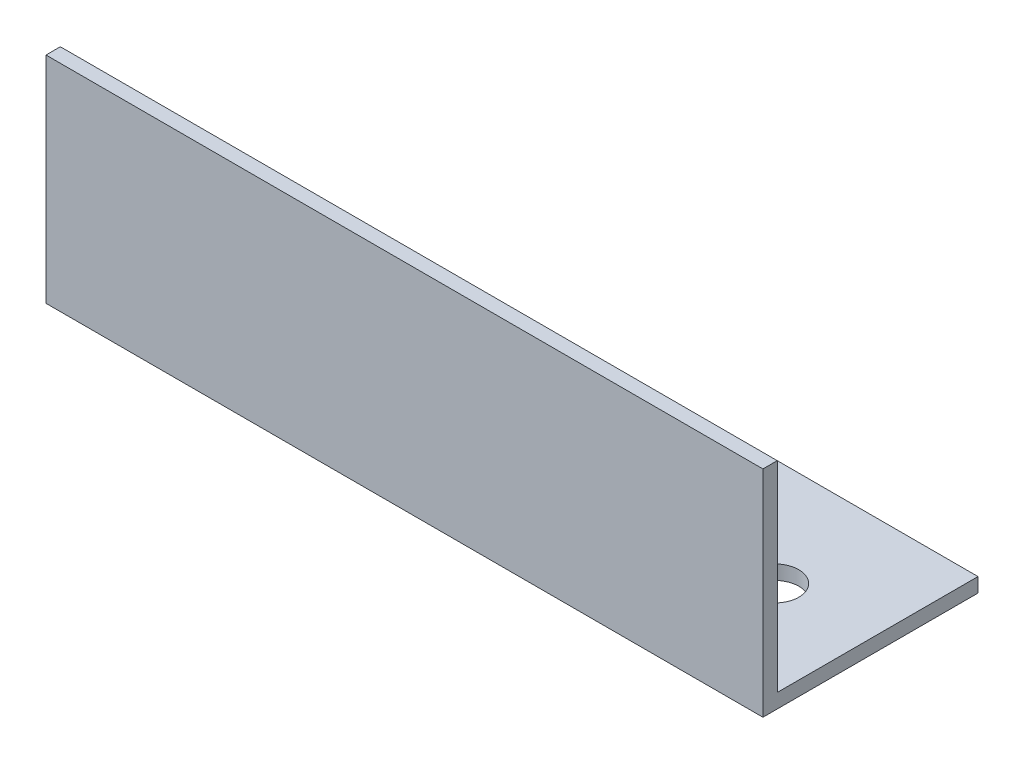
SolidWorks part; units mm, degrees
ref_plane "Спереди" through (0, 0, 0) normal (0, 0, 1) x (1, 0, 0)
ref_plane "Сверху" through (0, 0, 0) normal (0, 1, 0) x (1, 0, 0)
ref_plane "Справа" through (0, 0, 0) normal (1, 0, 0) x (0, 0, -1)
sketch "Эскиз1" plane through (0, 0, 0) normal (1, 0, 0) x (0, 0, -1)
  line L0 (0, 0) -> (0, 45)
  line L1 (0, 0) -> (45, 0)
  dimension "D1" = 45
extrude "Вытянуть-Тонкостенный1" add sketch "Эскиз1" along normal blind 150 thin
sketch "Эскиз2" plane through (0, 0, 0) normal (0, -1, 0) x (1, 0, 0)
  line L0 (150, -45) -> (0, -45) construction
  line L1 (0, 0) -> (0, -45) construction
  circle A0 centre (30, -22.5) radius 5
  circle A1 centre (130, -22.5) radius 5
  dimension "D1" = 22.5
  dimension "D3" = 10
  dimension "D2" = 30
  dimension "D4" = 2
extrude "Вырез-Вытянуть1" cut sketch "Эскиз2" against normal through all
